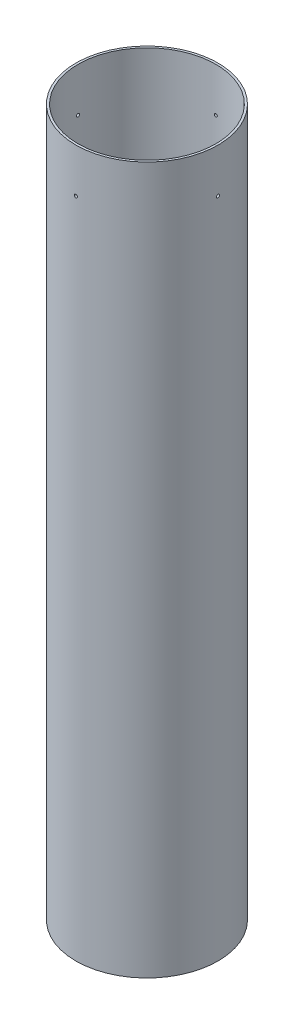
SolidWorks part; units mm, degrees
ref_plane "Front Plane" through (0, 0, 0) normal (0, 0, 1) x (1, 0, 0)
ref_plane "Top Plane" through (0, 0, 0) normal (0, 1, 0) x (1, 0, 0)
ref_plane "Right Plane" through (0, 0, 0) normal (1, 0, 0) x (0, 0, -1)
sketch "Sketch1" plane through (0, 0, 0) normal (0, 1, 0) x (1, 0, 0)
  circle A0 centre (0, 0) radius 51.1048
  circle A1 centre (0, 0) radius 49.53
  dimension "D1" = 102.2096
  dimension "D2" = 99.06
extrude "Boss-Extrude1" add sketch "Sketch1" along normal blind 508
sketch "Sketch2" plane through (0, 0, 0) normal (0, 0, 1) x (1, 0, 0)
  line L0 (49.53, 508) -> (-49.53, 508) construction
  line L1 (49.53, 508) -> (-49.53, 508) construction
  line L2 (0, 508) -> (0, 476.25) construction
  circle A0 centre (0, 476.25) radius 1.0922
  dimension "D2" = 2.1844
  dimension "D1" = 31.75
extrude "Cut-Extrude1" cut sketch "Sketch2" against normal through all
pattern_circular "CirPattern2" count 4 over 360 about axis through (0, 508, 0) along (0, -1, 0) of "Cut-Extrude1"
equation "\"Body_Tube_OD\"= 4.024in"
equation "\"Body_Tube_ID\"= 3.90in"
equation "\"D1@Sketch1\"=\"Body_Tube_OD\""
equation "\"D2@Sketch1\"=\"Body_Tube_ID\""
equation "\"Fwd_Section_Length\" = 20in"
equation "\"D1@Boss-Extrude1\"=\"Fwd_Section_Length\""
equation "\"Shear_Screw_Hole\" = 1.25in"
equation "\"Shear_Screw_Diameter\" = 0.086in"
equation "\"D1@Sketch2\"=\"Shear_Screw_Hole\""
equation "\"D2@Sketch2\"=\"Shear_Screw_Diameter\""
